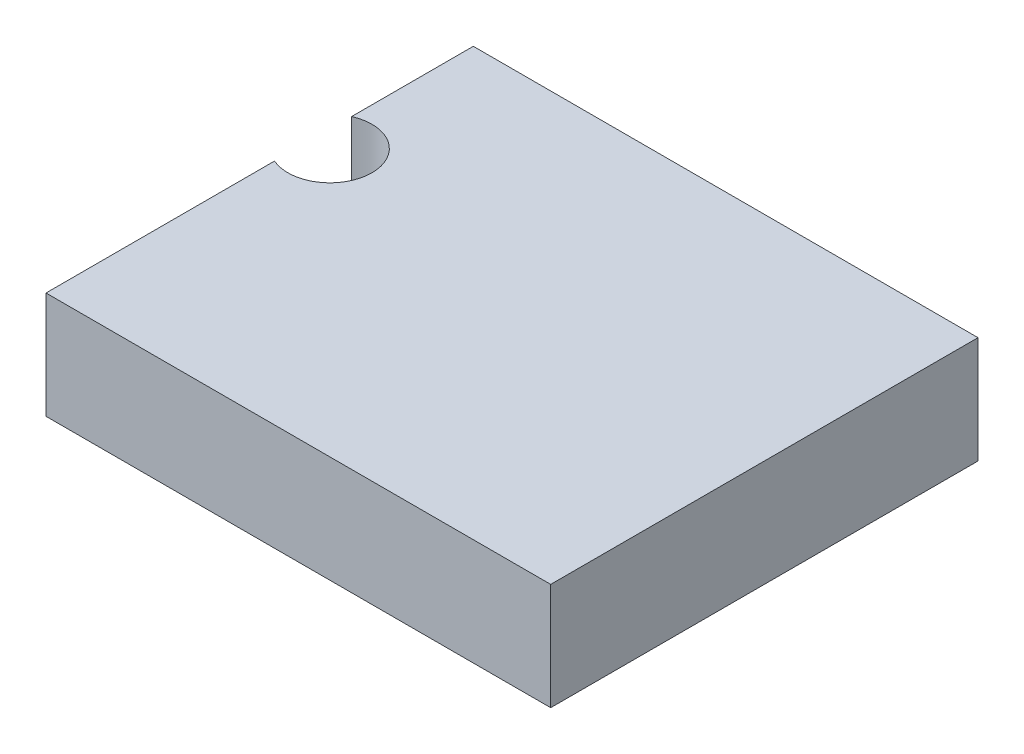
SolidWorks part; units mm, degrees
material "Acrylic (Medium-high impact)"
ref_plane "Front Plane" through (0, 0, 0) normal (0, 0, 1) x (1, 0, 0)
ref_plane "Top Plane" through (0, 0, 0) normal (0, 1, 0) x (1, 0, 0)
ref_plane "Right Plane" through (0, 0, 0) normal (1, 0, 0) x (0, 0, -1)
sketch "Sketch1" plane through (0, 0, 0) normal (0, 1, 0) x (1, 0, 0)
  line L1 (-15, -12.7) -> (15, -12.7)
  line L2 (-15, -12.7) -> (-15, 12.7)
  line L3 (-15, 12.7) -> (15, 12.7)
  line L4 (15, -12.7) -> (15, 12.7)
  line L5 (-15, -12.7) -> (15, 12.7) construction
  line L6 (-15, 12.7) -> (15, -12.7) construction
  point P0 (0, 0)
  dimension "D1" = 25.4
  dimension "D2" = 30
extrude "Boss-Extrude1" add sketch "Sketch1" along normal blind 6.35
sketch "Sketch2" plane through (0, 6.35, 0) normal (0, 1, 0) x (1, 0, 0)
  line L0 (-15, 12.7) -> (-15, -12.7) construction
  line L1 (-15, -12.7) -> (15, -12.7) construction
  circle A0 centre (-14, 3.175) radius 2.5
  dimension "D1" = 5
  dimension "D2" = 1
  dimension "D3" = 15.875
extrude "Cut-Extrude1" cut sketch "Sketch2" against normal through all
